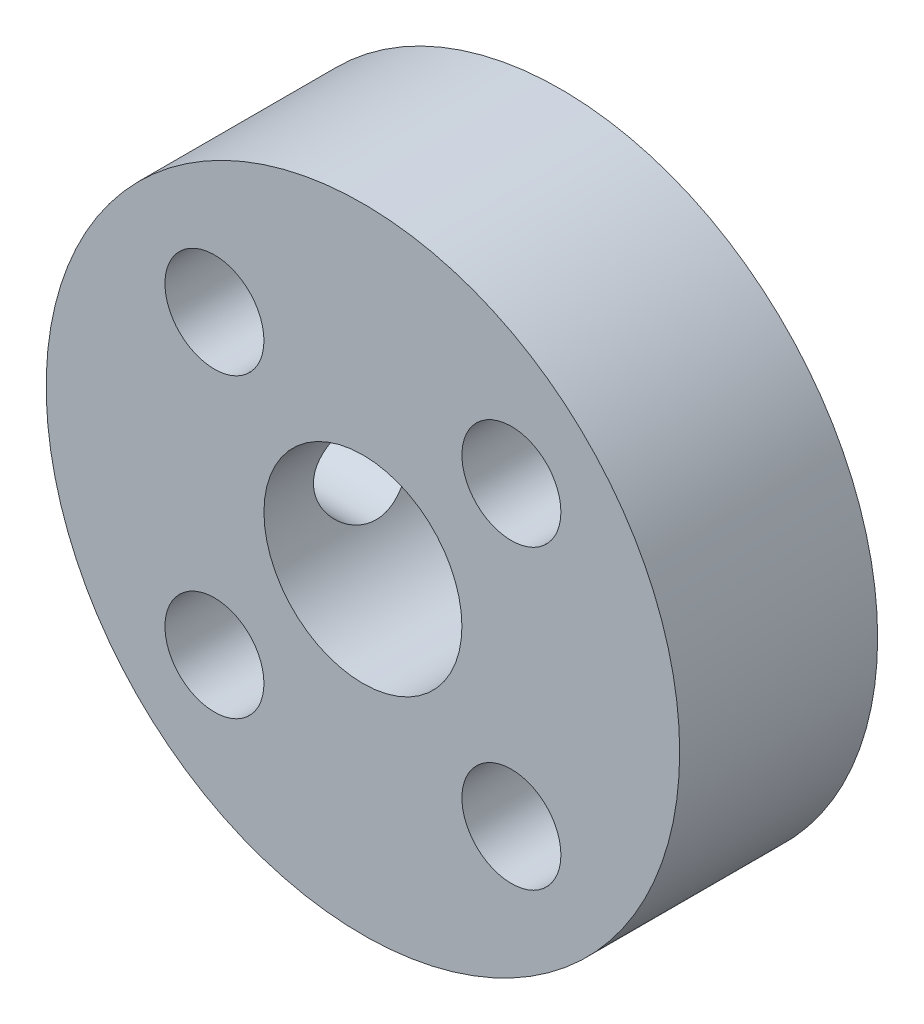
SolidWorks part; units mm, degrees
material "6061-T6 (SS)"
ref_plane "Front Plane" through (0, 0, 0) normal (0, 0, 1) x (1, 0, 0)
ref_plane "Top Plane" through (0, 0, 0) normal (0, 1, 0) x (1, 0, 0)
ref_plane "Right Plane" through (0, 0, 0) normal (1, 0, 0) x (0, 0, -1)
sketch "Sketch1" plane through (0, 0, 0) normal (0, 0, 1) x (1, 0, 0)
  line L1 (9.525, -9.525) -> (-9.525, -9.525) construction
  line L2 (9.525, -9.525) -> (9.525, 9.525) construction
  line L3 (9.525, 9.525) -> (-9.525, 9.525) construction
  line L4 (-9.525, -9.525) -> (-9.525, 9.525) construction
  line L5 (9.525, -9.525) -> (-9.525, 9.525) construction
  line L6 (9.525, 9.525) -> (-9.525, -9.525) construction
  circle A0 centre (0, 0) radius 6.35
  circle A1 centre (0, 0) radius 20.32
  circle A2 centre (-9.525, 9.525) radius 3.175
  circle A3 centre (9.525, 9.525) radius 3.175
  circle A4 centre (9.525, -9.525) radius 3.175
  circle A5 centre (-9.525, -9.525) radius 3.175
  dimension "D1" = 12.7
  dimension "D2" = 40.64
  dimension "D3" = 6.35
  dimension "D4" = 9.525
extrude "Boss-Extrude1" add sketch "Sketch1" along normal blind 12.7 contours A1 A5 A4 A3 A2 A0
sketch "Sketch2" plane through (0, 0, 0) normal (1, 0, 0) x (0, 0, -1)
  circle A0 centre (-6.35, 0) radius 3.175
  dimension "D1" = 6.35
  dimension "D2" = 6.35
extrude "Cut-Extrude1" cut sketch "Sketch2" against normal through all contours A0
